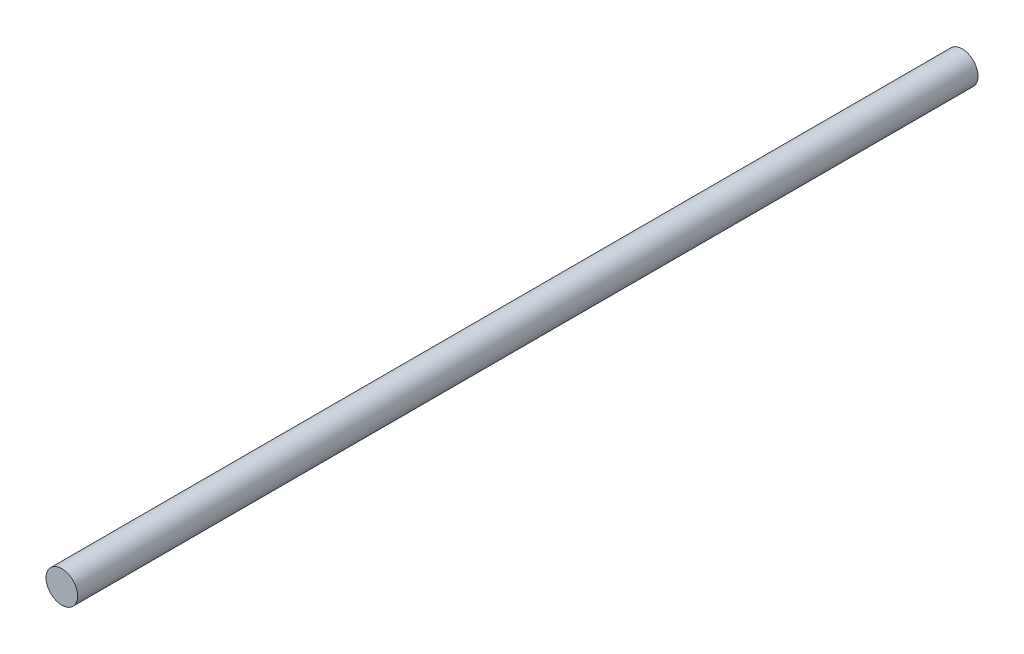
SolidWorks part; units mm, degrees
ref_plane "Front Plane" through (0, 0, 0) normal (0, 0, 1) x (1, 0, 0)
ref_plane "Top Plane" through (0, 0, 0) normal (0, 1, 0) x (1, 0, 0)
ref_plane "Right Plane" through (0, 0, 0) normal (1, 0, 0) x (0, 0, -1)
sketch "Sketch1" plane through (0, 0, 0) normal (0, 0, 1) x (1, 0, 0)
  circle A0 centre (0, 0) radius 4
  dimension "D1" = 8
extrude "Boss-Extrude1" add sketch "Sketch1" along normal blind 287.5
sketch "Sketch2" plane through (0, 0, 287.5) normal (0, 0, 1) x (1, 0, 0)
  circle A1 centre (0, 0) radius 4
  circle A2 centre (0, 0) radius 4
  dimension "D1" = 0
extrude "Boss-Extrude2" add sketch "Sketch2" along normal blind 45
sketch "Sketch3" plane through (0, 0, 0) normal (0, 0, -1) x (-1, 0, 0)
  circle A1 centre (0, 0) radius 4
  circle A2 centre (0, 0) radius 4
  dimension "D1" = 0
extrude "Cut-Extrude1" cut sketch "Sketch3" against normal blind 105
